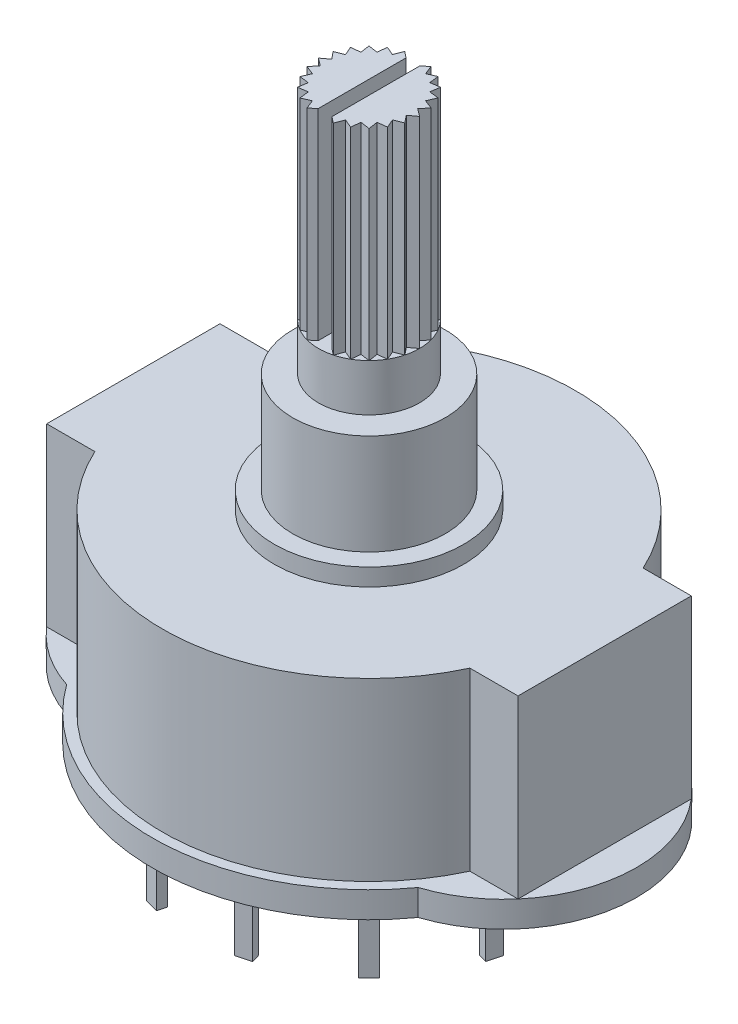
SolidWorks part; units mm, degrees
ref_plane "Front Plane" through (0, 0, 0) normal (0, 0, 1) x (1, 0, 0)
ref_plane "Top Plane" through (0, 0, 0) normal (0, 1, 0) x (1, 0, 0)
ref_plane "Right Plane" through (0, 0, 0) normal (1, 0, 0) x (0, 0, -1)
sketch "Sketch2" plane through (0, 0, 0) normal (0, 1, 0) x (1, 0, 0)
  line L0 (0, 0) -> (0, 6.8502) construction
  line L1 (-11.92, 0) -> (-11.92, -11.0081) construction
  line L2 (-22.4592, 6.8502) -> (24.2996, 6.8502) construction
  line L3 (-13.6, 5) -> (-13.6, -5)
  line L4 (-13.6, 5) -> (-10.8206, 5)
  line L5 (-13.6, -5) -> (-10.8206, -5)
  line L6 (13.6, -5) -> (10.8206, -5)
  line L7 (13.6, 5) -> (13.6, -5)
  line L8 (13.6, 5) -> (10.8206, 5)
  arc A0 (-10.8206, -5) -> (10.8206, -5) centre (0, 0) ccw
  arc A1 (10.8206, 5) -> (-10.8206, 5) centre (0, 0) ccw
  point P10 (-13.6, 0)
  dimension "D1" = 23.84
  dimension "D2" = 13.6
  dimension "D3" = 10
extrude "Boss-Extrude1" add sketch "Sketch2" along normal blind 10.15
sketch "Sketch3" plane through (0, 0, 0) normal (0, -1, 0) x (1, 0, 0)
  line L0 (-15.45, 4.934) -> (-15.45, -4.5404) construction
  line L1 (0, 0) -> (0, 4.4841) construction
  arc A0 (-10.143, -7.3055) -> (10.143, -7.3055) centre (0, 0) ccw
  arc A1 (-10.143, 7.3055) -> (-10.143, -7.3055) centre (-7.7682, 0) ccw
  arc A2 (10.143, 7.3055) -> (10.143, -7.3055) centre (7.7682, 0) cw
  arc A3 (10.143, 7.3055) -> (-10.143, 7.3055) centre (0, 0) ccw
  dimension "D2" = 25
  dimension "D1" = 15.45
extrude "Boss-Extrude2" add sketch "Sketch3" along normal blind 1.5
sketch "Sketch4" plane through (0, 10.15, 0) normal (0, 1, 0) x (1, 0, 0)
  circle A0 centre (0, 0) radius 5.46
  dimension "D1" = 10.92
extrude "Boss-Extrude3" add sketch "Sketch4" along normal blind 1
sketch "Sketch5" plane through (0, 11.15, 0) normal (0, 1, 0) x (1, 0, 0)
  circle A0 centre (0, 0) radius 4.4
  dimension "D1" = 8.8
extrude "Boss-Extrude4" add sketch "Sketch5" along normal blind 5.8
sketch "Sketch6" plane through (0, 16.95, 0) normal (0, 1, 0) x (1, 0, 0)
  circle A0 centre (0, 0) radius 2.915
  dimension "D1" = 5.83
extrude "Boss-Extrude5" add sketch "Sketch6" along normal blind 14.32
sketch "Sketch7" plane through (0, -1.5, 0) normal (0, -1, 0) x (1, 0, 0)
  line L0 (0, 0) -> (0, 11.5126) construction
  line L1 (0, 0) -> (5.7537, 9.9657) construction
  line L2 (0, 0) -> (2.9355, 10.9554) construction
  line L3 (2.1131, 9.5282) -> (2.9339, 9.3073)
  line L4 (2.1131, 9.5282) -> (0, 0) construction
  line L5 (0, 0) -> (2.9339, 9.3073) construction
  line L6 (2.1131, 9.5282) -> (2.243, 10.011)
  line L7 (2.9339, 9.3073) -> (3.0638, 9.7902)
  line L8 (2.243, 10.011) -> (3.0638, 9.7902)
  line L9 (6.948, 7.5483) -> (7.5484, 6.9466)
  line L10 (7.1945, 6.5934) -> (7.5484, 6.9466)
  line L11 (6.5941, 7.1951) -> (7.1945, 6.5934)
  line L12 (6.5941, 7.1951) -> (6.948, 7.5483)
  line L13 (9.7913, 3.063) -> (10.0104, 2.2417)
  line L14 (9.5273, 2.1128) -> (10.0104, 2.2417)
  line L15 (9.3082, 2.9341) -> (9.5273, 2.1128)
  line L16 (9.3082, 2.9341) -> (9.7913, 3.063)
  line L17 (10.011, -2.243) -> (9.7902, -3.0638)
  line L18 (9.3073, -2.9339) -> (9.7902, -3.0638)
  line L19 (9.5282, -2.1131) -> (9.3073, -2.9339)
  line L20 (9.5282, -2.1131) -> (10.011, -2.243)
  line L21 (7.5483, -6.948) -> (6.9466, -7.5484)
  line L22 (6.5934, -7.1945) -> (6.9466, -7.5484)
  line L23 (7.1951, -6.5941) -> (6.5934, -7.1945)
  line L24 (7.1951, -6.5941) -> (7.5483, -6.948)
  line L25 (3.063, -9.7913) -> (2.2417, -10.0104)
  line L26 (2.1128, -9.5273) -> (2.2417, -10.0104)
  line L27 (2.9341, -9.3082) -> (2.1128, -9.5273)
  line L28 (2.9341, -9.3082) -> (3.063, -9.7913)
  line L29 (-2.243, -10.011) -> (-3.0638, -9.7902)
  line L30 (-2.9339, -9.3073) -> (-3.0638, -9.7902)
  line L31 (-2.1131, -9.5282) -> (-2.9339, -9.3073)
  line L32 (-2.1131, -9.5282) -> (-2.243, -10.011)
  line L33 (-6.948, -7.5483) -> (-7.5484, -6.9466)
  line L34 (-7.1945, -6.5934) -> (-7.5484, -6.9466)
  line L35 (-6.5941, -7.1951) -> (-7.1945, -6.5934)
  line L36 (-6.5941, -7.1951) -> (-6.948, -7.5483)
  line L37 (-9.7913, -3.063) -> (-10.0104, -2.2417)
  line L38 (-9.5273, -2.1128) -> (-10.0104, -2.2417)
  line L39 (-9.3082, -2.9341) -> (-9.5273, -2.1128)
  line L40 (-9.3082, -2.9341) -> (-9.7913, -3.063)
  line L41 (-10.011, 2.243) -> (-9.7902, 3.0638)
  line L42 (-9.3073, 2.9339) -> (-9.7902, 3.0638)
  line L43 (-9.5282, 2.1131) -> (-9.3073, 2.9339)
  line L44 (-9.5282, 2.1131) -> (-10.011, 2.243)
  line L45 (-7.5483, 6.948) -> (-6.9466, 7.5484)
  line L46 (-6.5934, 7.1945) -> (-6.9466, 7.5484)
  line L47 (-7.1951, 6.5941) -> (-6.5934, 7.1945)
  line L48 (-7.1951, 6.5941) -> (-7.5483, 6.948)
  line L49 (-3.063, 9.7913) -> (-2.2417, 10.0104)
  line L50 (-2.1128, 9.5273) -> (-2.2417, 10.0104)
  line L51 (-2.9341, 9.3082) -> (-2.1128, 9.5273)
  line L52 (-2.9341, 9.3082) -> (-3.063, 9.7913)
  circle A0 centre (0, 0) radius 9.75 construction
  point P3 (2.5235, 9.4178)
  point P10 (2.5235, 9.4178)
  point P59 (0, 0)
  dimension "D1" = 19.5
  dimension "D2" = 30
  dimension "D3" = 15
  dimension "D4" = 0.85
  dimension "D5" = 87.567
  dimension "D6" = 0.5
  dimension "D7" = 0.5
  dimension "D8" = 12
extrude "Boss-Extrude6" add sketch "Sketch7" along normal blind 4.5
sketch "Sketch8" plane through (0, -1.5, 0) normal (0, -1, 0) x (1, 0, 0)
  line L0 (0, 0) -> (6.4, 0) construction
  line L1 (0, 0) -> (-6.4, 0) construction
  line L2 (-6.4, -0.425) -> (-6.4, 0.425)
  line L3 (-6.4, 0.425) -> (-5.9, 0.425)
  line L4 (-5.9, 0.425) -> (-5.9, -0.425)
  line L5 (-5.9, -0.425) -> (-6.4, -0.425)
  line L6 (0, 0) -> (0, 2.3383) construction
  line L7 (5.9, 0.425) -> (5.9, -0.425)
  line L8 (6.4, 0.425) -> (5.9, 0.425)
  line L9 (6.4, -0.425) -> (6.4, 0.425)
  line L10 (5.9, -0.425) -> (6.4, -0.425)
  point P7 (-6.4, 0)
  dimension "D1" = 12.8
  dimension "D2" = 6.4
  dimension "D3" = 0.85
  dimension "D4" = 0.5
extrude "Boss-Extrude7" add sketch "Sketch8" along normal blind 4.5
sketch "Sketch9" plane through (0, -1.5, 0) normal (0, -1, 0) x (1, 0, 0)
  circle A0 centre (0, 0) radius 2.8
  dimension "D1" = 5.6
extrude "Cut-Extrude1" cut sketch "Sketch9" against normal blind 4.5
sketch "Sketch11" plane through (0, 31.27, 0) normal (0, 1, 0) x (1, 0, 0)
  line L0 (0, 0) -> (0, 2.915) construction
  line L1 (0, 0) -> (0.75, 2.8169) construction
  line L2 (0, 0) -> (0.375, 2.8659) construction
  line L3 (0, 2.915) -> (0.75, 2.8169) construction
  line L4 (0, 2.915) -> (0.3244, 2.4789)
  line L5 (0.3244, 2.4789) -> (0.75, 2.8169)
  line L6 (0.7545, 2.8157) -> (0.9549, 2.3105)
  line L7 (0.9549, 2.3105) -> (1.4535, 2.5268)
  line L8 (1.4575, 2.5245) -> (1.5203, 1.9846)
  line L9 (1.5203, 1.9846) -> (2.058, 2.0645)
  line L10 (2.0612, 2.0612) -> (1.9822, 1.5235)
  line L11 (1.9822, 1.5235) -> (2.5222, 1.4615)
  line L12 (2.5245, 1.4575) -> (2.3089, 0.9585)
  line L13 (2.3089, 0.9585) -> (2.8145, 0.7589)
  line L14 (2.8157, 0.7545) -> (2.4784, 0.3283)
  line L15 (2.4784, 0.3283) -> (2.915, 0.0046)
  line L16 (2.915, 0) -> (2.4789, -0.3244)
  line L17 (2.4789, -0.3244) -> (2.8169, -0.75)
  line L18 (2.8157, -0.7545) -> (2.3105, -0.9549)
  line L19 (2.3105, -0.9549) -> (2.5268, -1.4535)
  line L20 (2.5245, -1.4575) -> (1.9846, -1.5203)
  line L21 (1.9846, -1.5203) -> (2.0645, -2.058)
  line L22 (2.0612, -2.0612) -> (1.5235, -1.9822)
  line L23 (1.5235, -1.9822) -> (1.4615, -2.5222)
  line L24 (1.4575, -2.5245) -> (0.9585, -2.3089)
  line L25 (0.9585, -2.3089) -> (0.7589, -2.8145)
  line L26 (0.7545, -2.8157) -> (0.3283, -2.4784)
  line L27 (0.3283, -2.4784) -> (0.0046, -2.915)
  line L28 (0, -2.915) -> (-0.3244, -2.4789)
  line L29 (-0.3244, -2.4789) -> (-0.75, -2.8169)
  line L30 (-0.7545, -2.8157) -> (-0.9549, -2.3105)
  line L31 (-0.9549, -2.3105) -> (-1.4535, -2.5268)
  line L32 (-1.4575, -2.5245) -> (-1.5203, -1.9846)
  line L33 (-1.5203, -1.9846) -> (-2.058, -2.0645)
  line L34 (-2.0612, -2.0612) -> (-1.9822, -1.5235)
  line L35 (-1.9822, -1.5235) -> (-2.5222, -1.4615)
  line L36 (-2.5245, -1.4575) -> (-2.3089, -0.9585)
  line L37 (-2.3089, -0.9585) -> (-2.8145, -0.7589)
  line L38 (-2.8157, -0.7545) -> (-2.4784, -0.3283)
  line L39 (-2.4784, -0.3283) -> (-2.915, -0.0046)
  line L40 (-2.915, 0) -> (-2.4789, 0.3244)
  line L41 (-2.4789, 0.3244) -> (-2.8169, 0.75)
  line L42 (-2.8157, 0.7545) -> (-2.3105, 0.9549)
  line L43 (-2.3105, 0.9549) -> (-2.5268, 1.4535)
  line L44 (-2.5245, 1.4575) -> (-1.9846, 1.5203)
  line L45 (-1.9846, 1.5203) -> (-2.0645, 2.058)
  line L46 (-2.0612, 2.0612) -> (-1.5235, 1.9822)
  line L47 (-1.5235, 1.9822) -> (-1.4615, 2.5222)
  line L48 (-1.4575, 2.5245) -> (-0.9585, 2.3089)
  line L49 (-0.9585, 2.3089) -> (-0.7589, 2.8145)
  line L50 (-0.7545, 2.8157) -> (-0.3283, 2.4784)
  line L51 (-0.3283, 2.4784) -> (-0.0046, 2.915)
  circle A3 centre (0, 0) radius 3.4876
  point P81 (0, 0)
  point P82 (0, 0)
  circle M3 centre (0, 0) radius 2.915
extrude "Cut-Extrude3" cut sketch "Sketch11" against normal blind 11.6 contours L46 L47 M3 | L48 L49 M3 | L50 L51 M3 | L4 L5 M3 | L6 L7 M3 | L8 L9 M3 | L10 L11 M3 | L12 L13 M3 | L14 L15 M3 | L16 L17 M3 | L18 L19 M3 | L20 L21 M3 | L22 L23 M3 | L24 L25 M3 | L26 L27 M3 | L28 L29 M3 | L30 L31 M3 | L32 L33 M3 | L34 L35 M3 | L36 L37 M3 | L38 L39 M3 | L40 L41 M3 | L42 L43 M3 | L44 L45 M3
sketch "Sketch10" plane through (0, 31.27, 0) normal (0, 1, 0) x (1, 0, 0)
  line L0 (0, 0) -> (0, 1.9628) construction
  line L1 (-0.4, 3.3912) -> (0.4, 3.3912)
  line L2 (0.4, 3.3912) -> (0.4, -3.3443)
  line L3 (0.4, -3.3443) -> (-0.4, -3.3443)
  line L4 (-0.4, -3.3443) -> (-0.4, 3.3912)
  dimension "D1" = 0.8
  dimension "D2" = 0.4
extrude "Cut-Extrude2" cut sketch "Sketch10" against normal blind 11.6
